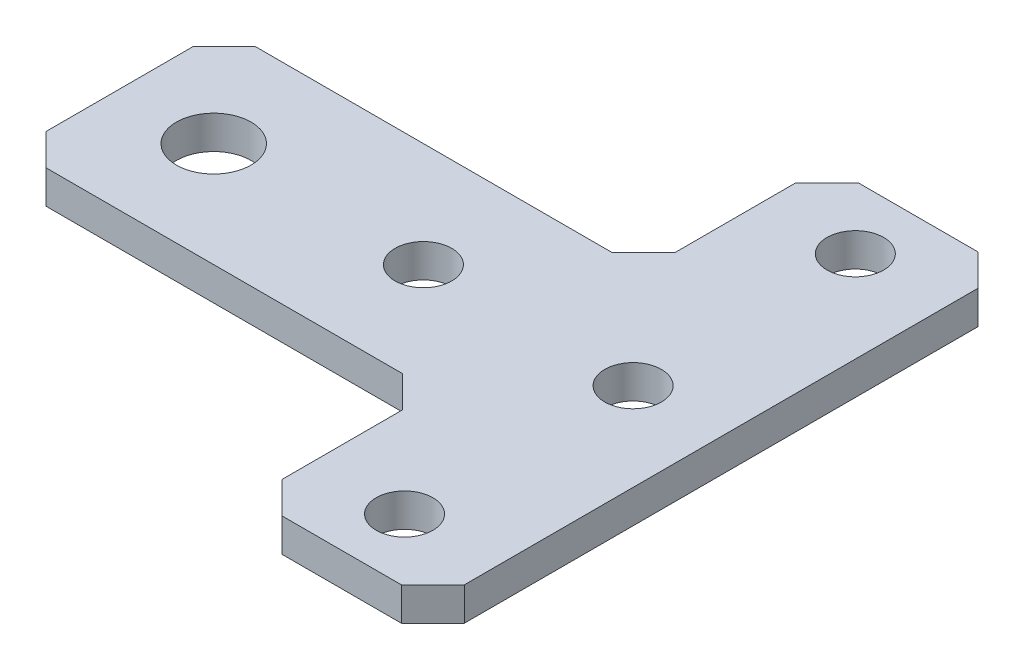
SolidWorks part; units mm, degrees
material "5052-H32"
ref_plane "Front Plane" through (0, 0, 0) normal (0, 0, 1) x (1, 0, 0)
ref_plane "Top Plane" through (0, 0, 0) normal (0, 1, 0) x (1, 0, 0)
ref_plane "Right Plane" through (0, 0, 0) normal (1, 0, 0) x (0, 0, -1)
sketch "Sketch1" plane through (0, 0, 0) normal (0, 1, 0) x (1, 0, 0)
  line L0 (57.4, 10) -> (0, 10) construction
  line L1 (0, 0) -> (40, 0)
  line L2 (0, 0) -> (0, 20)
  line L3 (0, 20) -> (40, 20)
  line L4 (48.7, 37.5) -> (48.7, -17.5) construction
  line L5 (40, -17.5) -> (57.4, -17.5)
  line L6 (40, -17.5) -> (40, 0)
  line L7 (40, 37.5) -> (57.4, 37.5)
  line L8 (57.4, -17.5) -> (57.4, 37.5)
  line L9 (40, 20) -> (40, 37.5)
  line L10 (19, 20) -> (19, 0) construction
  circle A0 centre (29, 10) radius 2.7
  circle A1 centre (9, 10) radius 3.56
  circle A2 centre (48.7, 31.5) radius 2.7
  circle A3 centre (48.7, -11.5) radius 2.7
  circle A4 centre (49, 10) radius 2.7
  dimension "D3" = 5.4
  dimension "D5" = 7.12
  dimension "D1" = 20
  dimension "D2" = 40
  dimension "D4" = 11
  dimension "D6" = 17.4
  dimension "D7" = 55
  dimension "D8" = 6
  dimension "D9" = 9
  dimension "D10" = 20
  dimension "D11" = 21
  dimension "D12" = 19.7
  dimension "D13" = 8.7
  dimension "D14" = 8.7
extrude "Boss-Extrude1" add sketch "Sketch1" along normal blind 3.175
chamfer "Chamfer1" distance 3 angle 45 6 edges at (57.4, 1.5875, 17.5) (40, 1.5875, 17.5) (0, 1.5875, 0) (57.4, 1.5875, -37.5) (40, 1.5875, -37.5) (0, 1.5875, -20)
chamfer "Chamfer2" distance 3 angle 45 2 edges at (40, 1.5875, 0) (40, 1.5875, -20)
sketch "Sketch3" plane through (0, 3.175, 0) normal (0, 1, 0) x (1, 0, 0)
  line L0 (21.8, 20) -> (21.8, 0) construction
  line L5 (21.8, 13) -> (21.8, 7) construction
  line L6 (23, 13) -> (23, 7)
  line L7 (20.6, 13) -> (20.6, 7)
  line L8 (16.8, 13) -> (16.8, 7) construction
  line L9 (3, 0) -> (37, 0) construction
  line L10 (0, 17) -> (0, 3) construction
  line L11 (37, 20) -> (3, 20) construction
  line L12 (18, 13) -> (18, 7)
  line L13 (15.6, 13) -> (15.6, 7)
  arc A0 (23, 13) -> (20.6, 13) centre (21.8, 13) ccw
  arc A1 (20.6, 7) -> (23, 7) centre (21.8, 7) ccw
  arc A2 (18, 13) -> (15.6, 13) centre (16.8, 13) ccw
  arc A3 (15.6, 7) -> (18, 7) centre (16.8, 7) ccw
  circle A4 centre (15.3, 17) radius 1.575
  circle A5 centre (15.3, 3) radius 1.575
  point P3 (21.8, 10)
  point P9 (21.8, 10)
  point P18 (16.8, 10)
  dimension "D2" = 1.2
  dimension "D5" = 1.2
  dimension "D9" = 3.15
  dimension "D1" = 21.8
  dimension "D3" = 6
  dimension "D4" = 5
  dimension "D6" = 6
  dimension "D7" = 1.5
  dimension "D8" = 7
  dimension "D10" = 14
